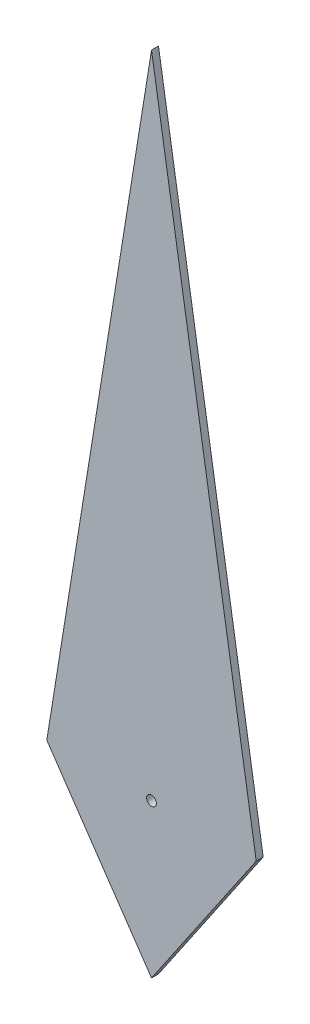
SolidWorks part; units mm, degrees
ref_plane "Front Plane" through (0, 0, 0) normal (0, 0, 1) x (1, 0, 0)
ref_plane "Top Plane" through (0, 0, 0) normal (0, 1, 0) x (1, 0, 0)
ref_plane "Right Plane" through (0, 0, 0) normal (1, 0, 0) x (0, 0, -1)
sketch "Sketch1" plane through (0, 0, 0) normal (0, 0, 1) x (1, 0, 0)
  line L0 (0, -0.943) -> (0, 8.369) construction
  line L1 (0, 8.369) -> (1.5, -0.943)
  line L2 (1.5, -0.943) -> (0, -3.1435)
  line L3 (-1.5, -0.943) -> (0, -3.1435)
  line L4 (0, 8.369) -> (-1.5, -0.943)
  circle A0 centre (0, -0.943) radius 0.07
  dimension "D1" = 3
extrude "Boss-Extrude1" add sketch "Sketch1" along normal blind 0.1
